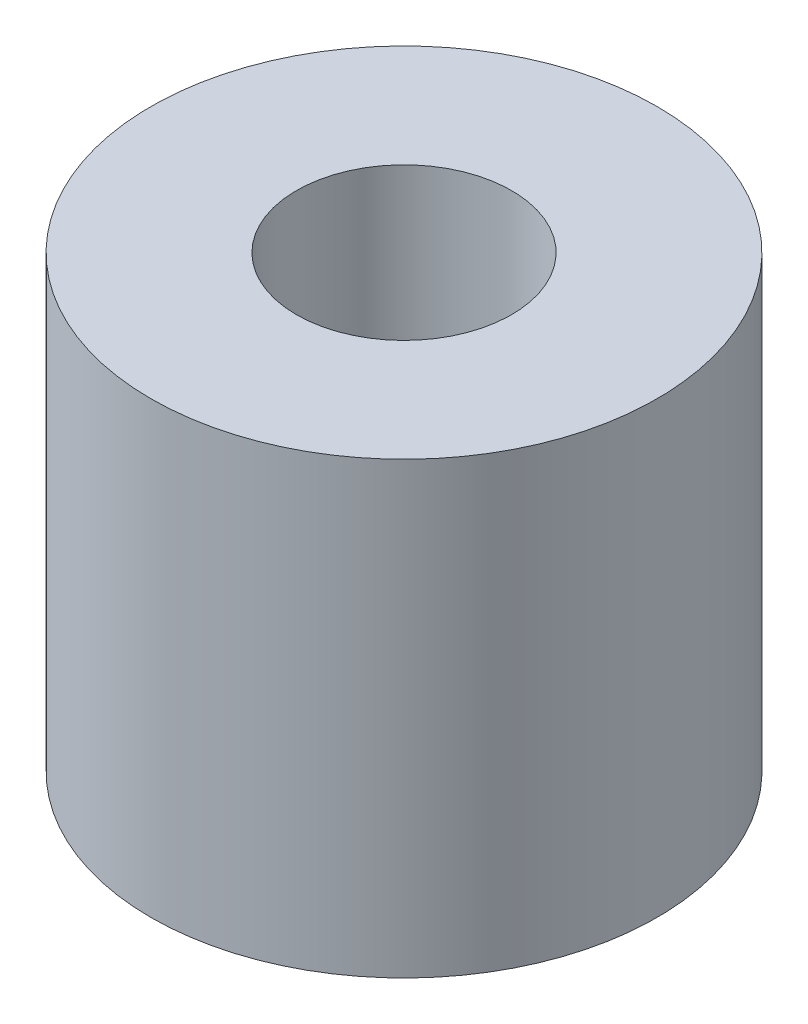
SolidWorks part; units mm, degrees
ref_plane "Front Plane" through (0, 0, 0) normal (0, 0, 1) x (1, 0, 0)
ref_plane "Top Plane" through (0, 0, 0) normal (0, 1, 0) x (1, 0, 0)
ref_plane "Right Plane" through (0, 0, 0) normal (1, 0, 0) x (0, 0, -1)
sketch "Sketch1" plane through (0, 0, 0) normal (0, 1, 0) x (1, 0, 0)
  circle A0 centre (0, 0) radius 1.7
  circle A1 centre (0, 0) radius 4
extrude "Boss-Extrude1" add sketch "Sketch1" along normal blind 7.1
